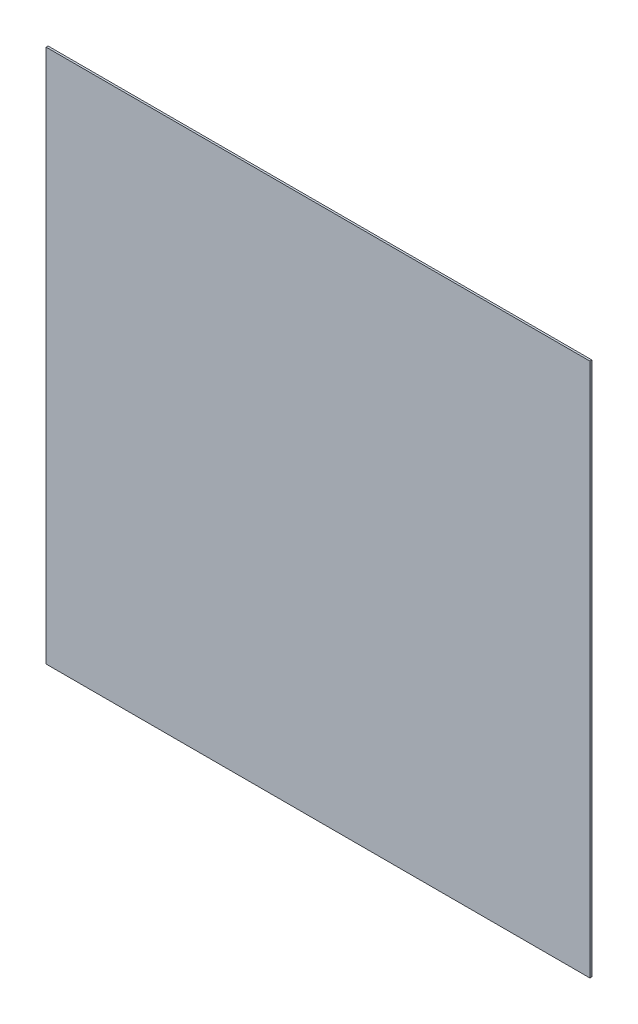
SolidWorks part; units mm, degrees
ref_plane "Front Plane" through (0, 0, 0) normal (0, 0, 1) x (1, 0, 0)
ref_plane "Top Plane" through (0, 0, 0) normal (0, 1, 0) x (1, 0, 0)
ref_plane "Right Plane" through (0, 0, 0) normal (1, 0, 0) x (0, 0, -1)
sketch "Sketch1" plane through (0, 0, 0) normal (0, 0, 1) x (1, 0, 0)
  line L1 (274.2406, -269.4781) -> (-274.2406, -269.4781)
  line L2 (274.2406, -269.4781) -> (274.2406, 269.4781)
  line L3 (274.2406, 269.4781) -> (-274.2406, 269.4781)
  line L4 (-274.2406, -269.4781) -> (-274.2406, 269.4781)
  line L5 (274.2406, -269.4781) -> (-274.2406, 269.4781) construction
  line L6 (274.2406, 269.4781) -> (-274.2406, -269.4781) construction
  point P0 (0, 0)
  dimension "D1" = 548.4813
  dimension "D2" = 538.9563
extrude "Boss-Extrude1" add sketch "Sketch1" along normal blind 2
